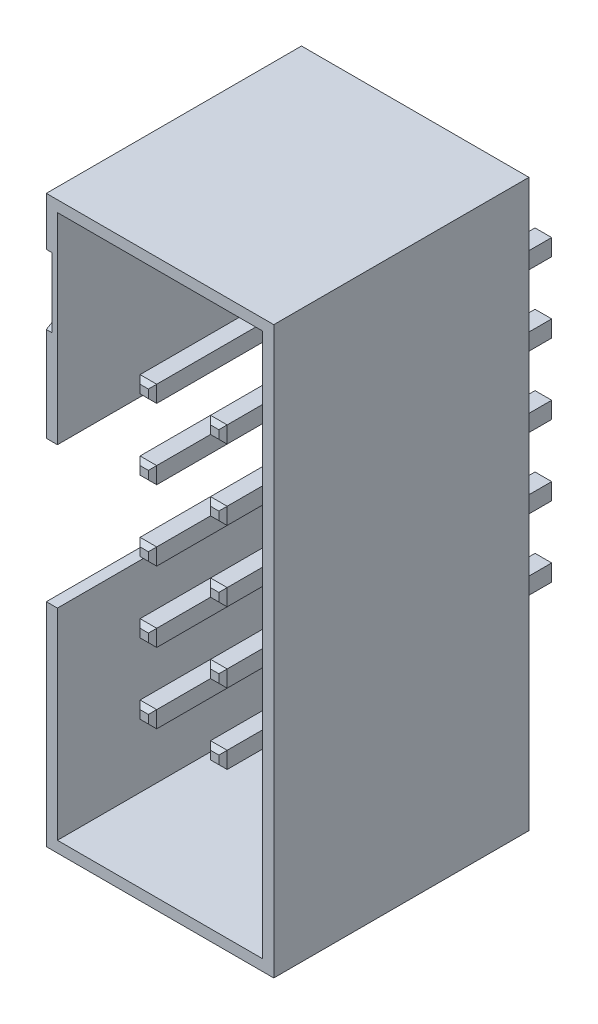
SolidWorks part; units mm, degrees
ref_plane "Plan de face" through (0, 0, 0) normal (0, 0, 1) x (1, 0, 0)
ref_plane "Plan de dessus" through (0, 0, 0) normal (0, 1, 0) x (1, 0, 0)
ref_plane "Plan de droite" through (0, 0, 0) normal (1, 0, 0) x (0, 0, -1)
sketch "Esquisse1" plane through (0, 0, 0) normal (0, 0, 1) x (1, 0, 0)
  line L1 (0, 0) -> (8.2, 0)
  line L2 (0, 0) -> (0, 20.4)
  line L3 (0, 20.4) -> (8.2, 20.4)
  line L4 (8.2, 0) -> (8.2, 20.4)
  dimension "D1" = 20.4
  dimension "D2" = 8.2
extrude "Boss.-Extru.1" add sketch "Esquisse1" along normal blind 9.2
sketch "Esquisse2" plane through (0, 0, 9.2) normal (0, 0, 1) x (1, 0, 0)
  line L0 (4.1, 10.2) -> (4.1, 20.4) construction
  line L1 (0.4, 0.4) -> (7.8, 0.4)
  line L2 (0.4, 0.4) -> (0.4, 20)
  line L3 (0.4, 20) -> (7.8, 20)
  line L4 (7.8, 0.4) -> (7.8, 20)
  line L5 (0.4, 0.4) -> (7.8, 20) construction
  line L6 (0.4, 20) -> (7.8, 0.4) construction
  line L7 (8.2, 20.4) -> (0, 20.4) construction
  line L8 (4.1, 10.2) -> (8.2, 10.2) construction
  line L9 (8.2, 0) -> (8.2, 20.4) construction
  line L10 (0, 20.4) -> (0, 0) construction
  point P0 (4.1, 10.2)
  dimension "D1" = 0.4
  dimension "D2" = 0.4
extrude "Enlèv. mat.-Extru.1" cut sketch "Esquisse2" against normal blind 8
sketch "Esquisse3" plane through (0, 0, 0) normal (0, 0, -1) x (-1, 0, 0)
  line L0 (-5.37, 15.28) -> (-8.2, 15.28) construction
  line L1 (-5.67, 15.58) -> (-5.07, 15.58)
  line L2 (-5.67, 15.58) -> (-5.67, 14.98)
  line L3 (-5.67, 14.98) -> (-5.07, 14.98)
  line L4 (-5.07, 15.58) -> (-5.07, 14.98)
  line L5 (-5.67, 15.58) -> (-5.07, 14.98) construction
  line L6 (-5.67, 14.98) -> (-5.07, 15.58) construction
  line L7 (-3.13, 15.58) -> (-2.53, 15.58)
  line L8 (-3.13, 15.58) -> (-3.13, 14.98)
  line L9 (-3.13, 14.98) -> (-2.53, 14.98)
  line L10 (-2.53, 15.58) -> (-2.53, 14.98)
  line L11 (-3.13, 15.58) -> (-2.53, 14.98) construction
  line L12 (-3.13, 14.98) -> (-2.53, 15.58) construction
  line L13 (-8.2, 0) -> (-8.2, 20.4) construction
  line L14 (-2.83, 15.28) -> (0, 15.28) construction
  line L15 (0, 20.4) -> (0, 0) construction
  line L16 (-5.37, 15.28) -> (-2.83, 15.28) construction
  line L17 (-5.67, 13.04) -> (-5.07, 13.04)
  line L18 (-5.67, 13.04) -> (-5.67, 12.44)
  line L19 (-5.67, 12.44) -> (-5.07, 12.44)
  line L20 (-5.07, 13.04) -> (-5.07, 12.44)
  line L21 (-3.13, 13.04) -> (-2.53, 13.04)
  line L22 (-3.13, 13.04) -> (-3.13, 12.44)
  line L23 (-3.13, 12.44) -> (-2.53, 12.44)
  line L24 (-2.53, 13.04) -> (-2.53, 12.44)
  line L25 (-5.37, 12.74) -> (-8.2, 12.74) construction
  line L26 (-5.67, 13.04) -> (-5.07, 12.44) construction
  line L27 (-5.67, 12.44) -> (-5.07, 13.04) construction
  line L28 (-3.13, 13.04) -> (-2.53, 12.44) construction
  line L29 (-3.13, 12.44) -> (-2.53, 13.04) construction
  line L30 (-2.83, 12.74) -> (0, 12.74) construction
  line L31 (-5.37, 12.74) -> (-2.83, 12.74) construction
  line L32 (-5.67, 10.5) -> (-5.07, 10.5)
  line L33 (-5.67, 10.5) -> (-5.67, 9.9)
  line L34 (-5.67, 9.9) -> (-5.07, 9.9)
  line L35 (-5.07, 10.5) -> (-5.07, 9.9)
  line L36 (-3.13, 10.5) -> (-2.53, 10.5)
  line L37 (-3.13, 10.5) -> (-3.13, 9.9)
  line L38 (-3.13, 9.9) -> (-2.53, 9.9)
  line L39 (-2.53, 10.5) -> (-2.53, 9.9)
  line L40 (-5.37, 10.2) -> (-8.2, 10.2) construction
  line L41 (-5.67, 10.5) -> (-5.07, 9.9) construction
  line L42 (-5.67, 9.9) -> (-5.07, 10.5) construction
  line L43 (-3.13, 10.5) -> (-2.53, 9.9) construction
  line L44 (-3.13, 9.9) -> (-2.53, 10.5) construction
  line L45 (-2.83, 10.2) -> (0, 10.2) construction
  line L46 (-5.37, 10.2) -> (-2.83, 10.2) construction
  line L47 (-5.67, 7.96) -> (-5.07, 7.96)
  line L48 (-5.67, 7.96) -> (-5.67, 7.36)
  line L49 (-5.67, 7.36) -> (-5.07, 7.36)
  line L50 (-5.07, 7.96) -> (-5.07, 7.36)
  line L51 (-3.13, 7.96) -> (-2.53, 7.96)
  line L52 (-3.13, 7.96) -> (-3.13, 7.36)
  line L53 (-3.13, 7.36) -> (-2.53, 7.36)
  line L54 (-2.53, 7.96) -> (-2.53, 7.36)
  line L55 (-5.37, 7.66) -> (-8.2, 7.66) construction
  line L56 (-5.67, 7.96) -> (-5.07, 7.36) construction
  line L57 (-5.67, 7.36) -> (-5.07, 7.96) construction
  line L58 (-3.13, 7.96) -> (-2.53, 7.36) construction
  line L59 (-3.13, 7.36) -> (-2.53, 7.96) construction
  line L60 (-2.83, 7.66) -> (0, 7.66) construction
  line L61 (-5.37, 7.66) -> (-2.83, 7.66) construction
  line L62 (-5.67, 5.42) -> (-5.07, 5.42)
  line L63 (-5.67, 5.42) -> (-5.67, 4.82)
  line L64 (-5.67, 4.82) -> (-5.07, 4.82)
  line L65 (-5.07, 5.42) -> (-5.07, 4.82)
  line L66 (-3.13, 5.42) -> (-2.53, 5.42)
  line L67 (-3.13, 5.42) -> (-3.13, 4.82)
  line L68 (-3.13, 4.82) -> (-2.53, 4.82)
  line L69 (-2.53, 5.42) -> (-2.53, 4.82)
  line L70 (-5.37, 5.12) -> (-8.2, 5.12) construction
  line L71 (-5.67, 5.42) -> (-5.07, 4.82) construction
  line L72 (-5.67, 4.82) -> (-5.07, 5.42) construction
  line L73 (-3.13, 5.42) -> (-2.53, 4.82) construction
  line L74 (-3.13, 4.82) -> (-2.53, 5.42) construction
  line L75 (-2.83, 5.12) -> (0, 5.12) construction
  line L76 (-5.37, 5.12) -> (-2.83, 5.12) construction
  line L77 (-5.37, 5.12) -> (-5.37, 0) construction
  line L78 (0, 0) -> (-8.2, 0) construction
  line L79 (-5.37, 15.28) -> (-5.37, 20.4) construction
  line L80 (-8.2, 20.4) -> (0, 20.4) construction
  point P0 (-5.37, 15.28)
  point P5 (-2.83, 15.28)
  point P20 (-5.37, 12.74)
  point P25 (-2.83, 12.74)
  point P34 (-5.37, 10.2)
  point P39 (-2.83, 10.2)
  point P48 (-5.37, 7.66)
  point P53 (-2.83, 7.66)
  point P62 (-5.37, 5.12)
  point P67 (-2.83, 5.12)
  dimension "D1" = 2.54
  dimension "D2" = 0.6
  dimension "D4" = 2.54
  dimension "D3" = 5
extrude "Boss.-Extru.2" add sketch "Esquisse3" along normal blind 3.5 and the other way blind 8.5
chamfer "Chanfrein1" distance 0.15 angle 45 80 edges at (5.37, 5.42, 8.5) (5.67, 5.12, 8.5) (5.37, 4.82, 8.5) (5.07, 5.12, 8.5) (5.37, 7.96, 8.5) (5.67, 7.66, 8.5) (5.37, 7.36, 8.5) (5.07, 7.66, 8.5) (5.37, 10.5, 8.5) (5.67, 10.2, 8.5) (5.37, 9.9, 8.5) (5.07, 10.2, 8.5) (5.37, 13.04, 8.5) (5.67, 12.74, 8.5) (5.37, 12.44, 8.5) (5.07, 12.74, 8.5) (5.37, 15.58, 8.5) (5.67, 15.28, 8.5) (5.37, 14.98, 8.5) (5.07, 15.28, 8.5) (2.83, 15.58, 8.5) (3.13, 15.28, 8.5) (2.83, 14.98, 8.5) (2.53, 15.28, 8.5) (2.83, 13.04, 8.5) (3.13, 12.74, 8.5) (2.83, 12.44, 8.5) (2.53, 12.74, 8.5) (2.83, 10.5, 8.5) (3.13, 10.2, 8.5) (2.83, 9.9, 8.5) (2.53, 10.2, 8.5) (2.83, 7.96, 8.5) (3.13, 7.66, 8.5) (2.83, 7.36, 8.5) (2.53, 7.66, 8.5) (2.83, 5.42, 8.5) (3.13, 5.12, 8.5) (2.83, 4.82, 8.5) (2.53, 5.12, 8.5) (2.83, 4.82, -3.5) (3.13, 5.12, -3.5) (2.83, 5.42, -3.5) (2.53, 5.12, -3.5) (5.37, 4.82, -3.5) (5.67, 5.12, -3.5) (5.37, 5.42, -3.5) (5.07, 5.12, -3.5) (5.37, 7.36, -3.5) (5.67, 7.66, -3.5) (5.37, 7.96, -3.5) (5.07, 7.66, -3.5) (2.83, 7.36, -3.5) (3.13, 7.66, -3.5) (2.83, 7.96, -3.5) (2.53, 7.66, -3.5) (2.83, 9.9, -3.5) (3.13, 10.2, -3.5) (2.83, 10.5, -3.5) (2.53, 10.2, -3.5) (5.37, 9.9, -3.5) (5.67, 10.2, -3.5) (5.37, 10.5, -3.5) (5.07, 10.2, -3.5) (5.37, 12.44, -3.5) (5.67, 12.74, -3.5) (5.37, 13.04, -3.5) (5.07, 12.74, -3.5) (2.83, 12.44, -3.5) (3.13, 12.74, -3.5) (2.83, 13.04, -3.5) (2.53, 12.74, -3.5) (2.83, 14.98, -3.5) (3.13, 15.28, -3.5) (2.83, 15.58, -3.5) (2.53, 15.28, -3.5) (5.37, 14.98, -3.5) (5.67, 15.28, -3.5) (5.37, 15.58, -3.5) (5.07, 15.28, -3.5)
sketch "Esquisse4" plane through (0, 0, 9.2) normal (0, 0, 1) x (1, 0, 0)
  line L0 (0, 20.4) -> (0, 0) construction
  line L1 (0, 12.75) -> (0.4, 12.75)
  line L2 (0, 12.75) -> (0, 7.65)
  line L3 (0, 7.65) -> (0.4, 7.65)
  line L4 (0.4, 12.75) -> (0.4, 7.65)
  line L5 (0.4, 20) -> (0.4, 0.4) construction
  line L6 (0, 0) -> (0, 7.65) construction
  line L7 (0, 20.4) -> (0, 12.75) construction
  dimension "D1" = 5.1
extrude "Enlèv. mat.-Extru.2" cut sketch "Esquisse4" against normal up to surface (8 mm away) up to face at (2.83, 5.12, 1.2)
sketch "Esquisse5" plane through (0, 0, 0) normal (-1, 0, 0) x (0, 0, 1)
  line L0 (9.2, 18.65) -> (9.2, 16.15)
  line L1 (9.2, 20.4) -> (9.2, 12.75) construction
  line L2 (9.2, 16.15) -> (7.0349, 17.4)
  line L3 (7.0349, 17.4) -> (9.2, 18.65)
  line L4 (9.2, 20.4) -> (0, 20.4) construction
  dimension "D1" = 2.5
  dimension "D2" = 3
extrude "Enlèv. mat.-Extru.3" cut sketch "Esquisse5" against normal blind 0.2
